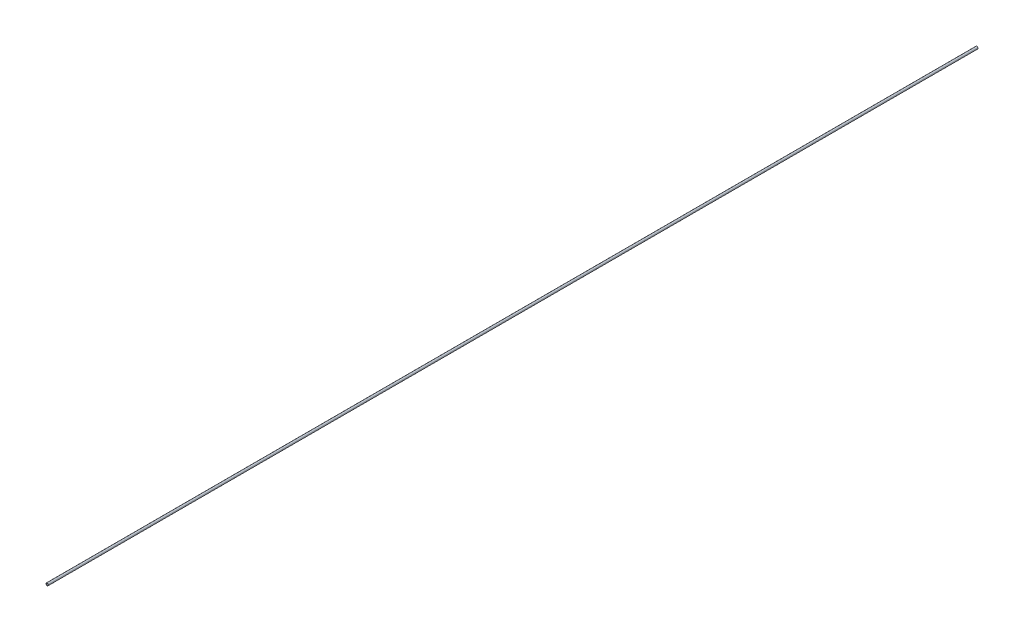
SolidWorks part; units mm, degrees
ref_plane "Front" through (0, 0, 0) normal (0, 0, 1) x (1, 0, 0)
ref_plane "Top" through (0, 0, 0) normal (0, 1, 0) x (1, 0, 0)
ref_plane "Right" through (0, 0, 0) normal (1, 0, 0) x (0, 0, -1)
sketch "Sketch1" plane through (0, 0, 0) normal (0, 0, 1) x (1, 0, 0)
  circle A0 centre (0, 0) radius 1.6
  circle A1 centre (0, 0) radius 2.5
extrude "Boss-Extrude1" add sketch "Sketch1" along normal blind 1000
sketch "Sketch2" plane through (0, 0, 1000) normal (0, 0, 1) x (1, 0, 0)
  circle A0 centre (0, 0) radius 1.6
  circle A1 centre (0, 0) radius 2.5
extrude "Boss-Extrude2" add sketch "Sketch2" along normal blind 500
sketch "Sketch3" plane through (0, 0, 1500) normal (0, 0, 1) x (1, 0, 0)
  circle A0 centre (0, 0) radius 1.6
  circle A1 centre (0, 0) radius 2.5
extrude "Boss-Extrude3" add sketch "Sketch3" along normal blind 500
